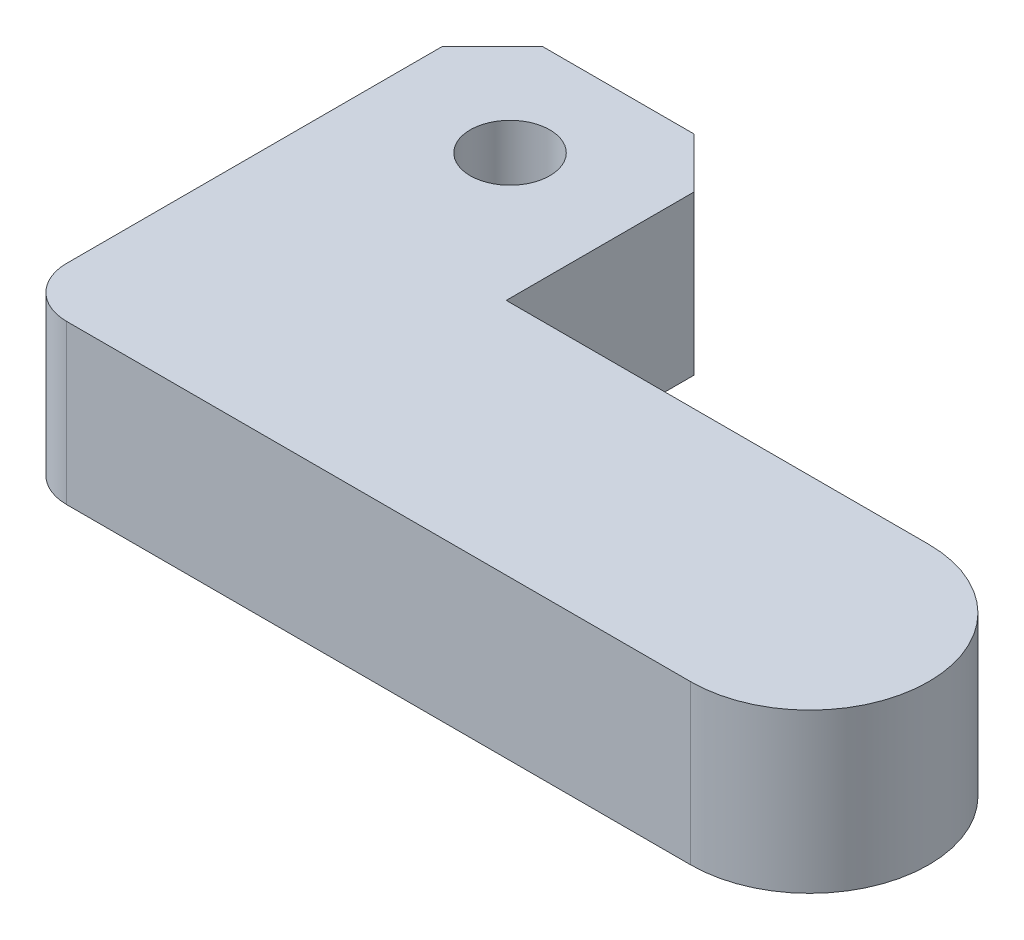
SolidWorks part; units mm, degrees
material "6061 Alloy"
ref_plane "Front" through (0, 0, 0) normal (0, 0, 1) x (1, 0, 0)
ref_plane "Top" through (0, 0, 0) normal (0, 1, 0) x (1, 0, 0)
ref_plane "Right" through (0, 0, 0) normal (1, 0, 0) x (0, 0, -1)
sketch "Sketch1" plane through (0, 0, 0) normal (0, 1, 0) x (1, 0, 0)
  line L0 (0, 30) -> (0, 0)
  line L1 (0, 0) -> (42.5, 0)
  line L3 (42.5, 15) -> (15.875, 15)
  line L4 (15.875, 15) -> (15.875, 30)
  line L5 (15.875, 30) -> (0, 30)
  circle A0 centre (7.9375, 23.175) radius 2.5082
  arc A1 (42.5, 0) -> (42.5, 15) centre (42.5, 7.5) ccw
  point P10 (7.9375, 30)
  point P14 (50, 0)
  dimension "D4" = 5.0165
  dimension "D6" = 7.5
  dimension "D5" = 8.175
  dimension "D3" = 50
  dimension "D1" = 15.875
  dimension "D2" = 30
  dimension "D7" = 15
extrude "Boss-Extrude1" add sketch "Sketch1" along normal blind 10
fillet "Fillet1" radius 3.175 1 edges at (0, 5, 0)
chamfer "Chamfer1" distance 3.175 angle 45 2 edges at (0, 5, -30) (15.875, 5, -30)
